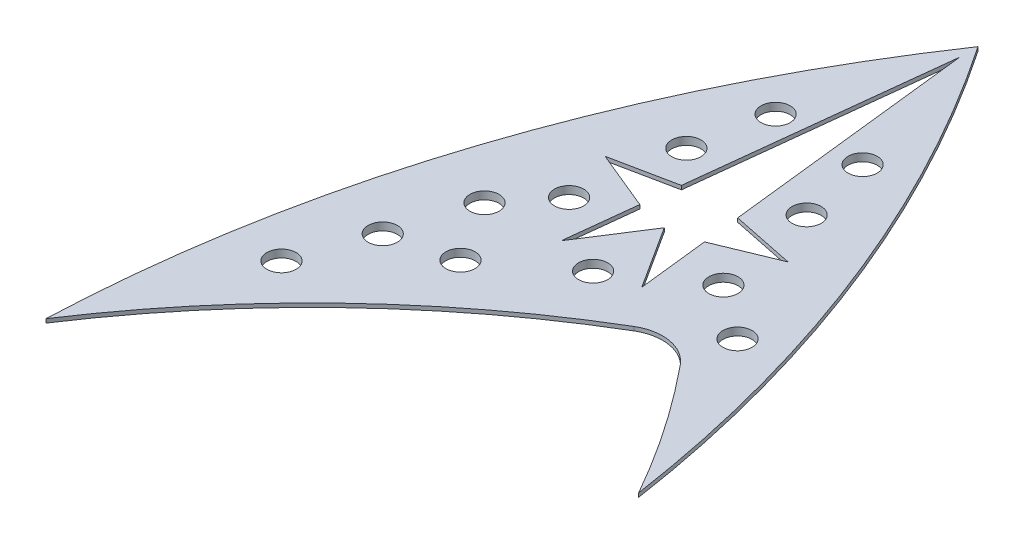
SolidWorks part; units mm, degrees
ref_plane "Front Plane" through (0, 0, 0) normal (0, 0, 1) x (1, 0, 0)
ref_plane "Top Plane" through (0, 0, 0) normal (0, 1, 0) x (1, 0, 0)
ref_plane "Right Plane" through (0, 0, 0) normal (1, 0, 0) x (0, 0, -1)
sketch "Sketch2" plane through (0, 0, 0) normal (0, 1, 0) x (1, 0, 0)
  line L10 (29.7241, 45.5525) -> (30.5369, 38.3256)
  line L11 (36.632, 48.4021) -> (29.7241, 45.5525)
  line L12 (29.1261, 50.8699) -> (35.6287, 49.5371)
  line L13 (26.9138, 70.5394) -> (29.1261, 50.8699)
  line L14 (21.5114, 50.8699) -> (23.7236, 70.5394)
  line L15 (15.0087, 49.5371) -> (21.5114, 50.8699)
  line L16 (20.9133, 45.5525) -> (14.0054, 48.4021)
  line L17 (19.7009, 34.7729) -> (20.9133, 45.5525)
  line L18 (25.3187, 43.524) -> (19.7009, 34.7729)
  line L19 (29.371, 37.2116) -> (25.3187, 43.524)
  line L29 (22.4239, 50.0361) -> (25.3187, 75.7743)
  line L30 (25.3187, 75.7743) -> (28.2135, 50.0361)
  line L31 (28.2135, 50.0361) -> (34.732, 48.7001)
  line L32 (34.732, 48.7001) -> (28.6462, 46.1896)
  line L33 (28.6462, 46.1896) -> (29.464, 38.9178)
  line L34 (29.464, 38.9178) -> (25.3187, 45.3751)
  line L35 (25.3187, 45.3751) -> (21.1734, 38.9178)
  line L36 (21.1734, 38.9178) -> (21.9913, 46.1896)
  line L37 (21.9913, 46.1896) -> (15.9054, 48.7001)
  line L39 (15.9054, 48.7001) -> (22.4239, 50.0361)
  arc A5 (47.6216, 20.4347) -> (38.3331, 34.0133) centre (-35, -26.1166) ccw
  arc A6 (38.3331, 34.0133) -> (32.5601, 35.0318) centre (34.8534, 31.16) ccw
  arc A7 (32.5601, 35.0318) -> (1.6083, 5.4751) centre (80.8889, -46.5628) ccw
  arc A8 (47.6216, 20.4347) -> (25.3187, 77.656) centre (-89.3626, 0) ccw
  arc A9 (25.3187, 77.656) -> (1.6083, 5.4751) centre (140, 0) ccw
  arc A23 (30.5369, 38.3256) -> (31.946, 37.5277) centre (31.5307, 38.4374) ccw
  arc A24 (42.6939, 32.5131) -> (40.2664, 35.5985) centre (-35, -26.1166) ccw
  arc A25 (40.2664, 35.5985) -> (31.946, 37.5277) centre (34.8534, 31.16) ccw
  arc A26 (42.6939, 32.5131) -> (37.9494, 47.8294) centre (-89.3626, 0) ccw
  arc A27 (37.9494, 47.8294) -> (36.632, 48.4021) centre (37.0133, 47.4777) ccw
  arc A28 (35.6287, 49.5371) -> (36.7569, 50.8909) centre (35.8295, 50.5167) ccw
  arc A29 (36.7569, 50.8909) -> (26.9138, 70.5394) centre (-89.3626, 0) ccw
  arc A30 (23.7236, 70.5394) -> (13.8806, 50.8909) centre (140, 0) ccw
  arc A31 (13.8806, 50.8909) -> (15.0087, 49.5371) centre (14.8079, 50.5167) ccw
  arc A32 (29.0619, 35.8249) -> (29.371, 37.2116) centre (28.5294, 36.6714) ccw
  arc A33 (29.0619, 35.8249) -> (4.727, 14.0437) centre (80.8889, -46.5628) ccw
  arc A34 (12.688, 47.8294) -> (4.727, 14.0437) centre (140, 0) ccw
  arc A35 (14.0054, 48.4021) -> (12.688, 47.8294) centre (13.6241, 47.4777) ccw
sketch "Sketch3" plane through (0, 0, 0) normal (0, 1, 0) x (1, 0, 0)
  point P0 (8.58, 22.733)
  point P1 (11.374, 30.353)
  point P3 (13.843, 38.354)
  point P4 (17.724, 43.18)
  point P5 (17.724, 32.004)
  point P6 (25.527, 37.846)
  point P7 (33.472, 43.307)
  point P8 (38.989, 39.243)
  point P9 (19.375, 53.594)
  point P10 (29.901, 61.2)
  point P11 (31.496, 53.848)
  point P12 (20.925, 61.225)
  dimension "D1" = 22.733
  dimension "D2" = 8.58
  dimension "D3" = 30.353
  dimension "D4" = 11.374
  dimension "D5" = 43.18
  dimension "D6" = 17.724
  dimension "D7" = 32.004
  dimension "D8" = 17.724
  dimension "D9" = 38.354
  dimension "D10" = 13.843
  dimension "D11" = 37.846
  dimension "D12" = 25.527
  dimension "D13" = 43.307
  dimension "D14" = 33.472
  dimension "D15" = 39.243
  dimension "D16" = 38.989
  dimension "D17" = 53.848
  dimension "D18" = 31.496
  dimension "D19" = 19.375
  dimension "D20" = 53.594
  dimension "D21" = 61.225
  dimension "D22" = 20.925
  dimension "D23" = 29.901
  dimension "D24" = 61.2
sketch "Sketch4" plane through (0, 0, 0) normal (0, 1, 0) x (1, 0, 0)
  line L0 (36.632, 48.4021) -> (29.7241, 45.5525) construction
  line L1 (29.7241, 45.5525) -> (30.5369, 38.3256) construction
  line L2 (26.9138, 70.5394) -> (29.1261, 50.8699) construction
  line L3 (29.1261, 50.8699) -> (35.6287, 49.5371) construction
  line L4 (20.9133, 45.5525) -> (14.0054, 48.4021) construction
  line L5 (29.371, 37.2116) -> (25.3187, 43.524) construction
  line L6 (25.3187, 43.524) -> (19.7009, 34.7729) construction
  line L7 (19.7009, 34.7729) -> (20.9133, 45.5525) construction
  line L8 (15.0087, 49.5371) -> (21.5114, 50.8699) construction
  line L9 (21.5114, 50.8699) -> (23.7236, 70.5394) construction
  line L10 (36.632, 48.4021) -> (29.7241, 45.5525)
  line L11 (29.7241, 45.5525) -> (30.5369, 38.3256)
  line L12 (26.9138, 70.5394) -> (29.1261, 50.8699)
  line L13 (29.1261, 50.8699) -> (35.6287, 49.5371)
  line L14 (20.9133, 45.5525) -> (14.0054, 48.4021)
  line L15 (29.371, 37.2116) -> (25.3187, 43.524)
  line L16 (25.3187, 43.524) -> (19.7009, 34.7729)
  line L17 (19.7009, 34.7729) -> (20.9133, 45.5525)
  line L18 (15.0087, 49.5371) -> (21.5114, 50.8699)
  line L19 (21.5114, 50.8699) -> (23.7236, 70.5394)
  arc A0 (30.5369, 38.3256) -> (31.946, 37.5277) centre (31.5307, 38.4374) ccw construction
  arc A1 (40.2664, 35.5985) -> (31.946, 37.5277) centre (34.8534, 31.16) ccw construction
  arc A2 (42.6939, 32.5131) -> (40.2664, 35.5985) centre (-35, -26.1166) ccw construction
  arc A3 (42.6939, 32.5131) -> (37.9494, 47.8294) centre (-89.3626, 0) ccw construction
  arc A4 (37.9494, 47.8294) -> (36.632, 48.4021) centre (37.0133, 47.4777) ccw construction
  arc A5 (35.6287, 49.5371) -> (36.7569, 50.8909) centre (35.8295, 50.5167) ccw construction
  arc A6 (36.7569, 50.8909) -> (26.9138, 70.5394) centre (-89.3626, 0) ccw construction
  arc A7 (14.0054, 48.4021) -> (12.688, 47.8294) centre (13.6241, 47.4777) ccw construction
  arc A8 (12.688, 47.8294) -> (4.727, 14.0437) centre (140, 0) ccw construction
  arc A9 (29.0619, 35.8249) -> (4.727, 14.0437) centre (80.8889, -46.5628) ccw construction
  arc A10 (29.0619, 35.8249) -> (29.371, 37.2116) centre (28.5294, 36.6714) ccw construction
  arc A11 (13.8806, 50.8909) -> (15.0087, 49.5371) centre (14.8079, 50.5167) ccw construction
  arc A12 (23.7236, 70.5394) -> (13.8806, 50.8909) centre (140, 0) ccw construction
  arc A13 (30.5369, 38.3256) -> (31.946, 37.5277) centre (31.5307, 38.4374) ccw
  arc A14 (40.2664, 35.5985) -> (31.946, 37.5277) centre (34.8534, 31.16) ccw
  arc A15 (42.6939, 32.5131) -> (40.2664, 35.5985) centre (-35, -26.1166) ccw
  arc A16 (42.6939, 32.5131) -> (37.9494, 47.8294) centre (-89.3626, 0) ccw
  arc A17 (37.9494, 47.8294) -> (36.632, 48.4021) centre (37.0133, 47.4777) ccw
  arc A18 (35.6287, 49.5371) -> (36.7569, 50.8909) centre (35.8295, 50.5167) ccw
  arc A19 (36.7569, 50.8909) -> (26.9138, 70.5394) centre (-89.3626, 0) ccw
  arc A20 (14.0054, 48.4021) -> (12.688, 47.8294) centre (13.6241, 47.4777) ccw
  arc A21 (12.688, 47.8294) -> (4.727, 14.0437) centre (140, 0) ccw
  arc A22 (29.0619, 35.8249) -> (4.727, 14.0437) centre (80.8889, -46.5628) ccw
  arc A23 (29.0619, 35.8249) -> (29.371, 37.2116) centre (28.5294, 36.6714) ccw
  arc A24 (13.8806, 50.8909) -> (15.0087, 49.5371) centre (14.8079, 50.5167) ccw
  arc A25 (23.7236, 70.5394) -> (13.8806, 50.8909) centre (140, 0) ccw
  circle A26 centre (8.58, 22.733) radius 1.5
  circle A27 centre (11.374, 30.353) radius 1.5
  circle A28 centre (13.843, 38.354) radius 1.5
  circle A29 centre (17.724, 32.004) radius 1.5
  circle A30 centre (17.724, 43.18) radius 1.5
  circle A31 centre (19.375, 53.594) radius 1.5
  circle A32 centre (20.925, 61.225) radius 1.5
  circle A33 centre (33.472, 43.307) radius 1.5
  circle A34 centre (38.989, 39.243) radius 1.5
  circle A35 centre (31.496, 53.848) radius 1.5
  circle A36 centre (29.901, 61.2) radius 1.5
  circle A37 centre (25.527, 37.846) radius 1.5
extrude "Boss-Extrude1" add sketch "Sketch4" along normal blind 0.4
sketch "Sketch5" plane through (0, 0.4, 0) normal (0, 1, 0) x (1, 0, 0)
  line L0 (22.4239, 50.0361) -> (25.3187, 75.7743) construction
  line L1 (25.3187, 75.7743) -> (28.2135, 50.0361) construction
  line L2 (28.2135, 50.0361) -> (34.732, 48.7001) construction
  line L3 (34.732, 48.7001) -> (28.6462, 46.1896) construction
  line L4 (28.6462, 46.1896) -> (29.464, 38.9178) construction
  line L5 (29.464, 38.9178) -> (25.3187, 45.3751) construction
  line L6 (25.3187, 45.3751) -> (21.1734, 38.9178) construction
  line L7 (21.1734, 38.9178) -> (21.9913, 46.1896) construction
  line L8 (21.9913, 46.1896) -> (15.9054, 48.7001) construction
  line L9 (15.9054, 48.7001) -> (22.4239, 50.0361) construction
  line L10 (22.4239, 50.0361) -> (25.3187, 75.7743)
  line L11 (25.3187, 75.7743) -> (28.2135, 50.0361)
  line L12 (28.2135, 50.0361) -> (34.732, 48.7001)
  line L13 (34.732, 48.7001) -> (28.6462, 46.1896)
  line L14 (28.6462, 46.1896) -> (29.464, 38.9178)
  line L15 (29.464, 38.9178) -> (25.3187, 45.3751)
  line L16 (25.3187, 45.3751) -> (21.1734, 38.9178)
  line L17 (21.1734, 38.9178) -> (21.9913, 46.1896)
  line L18 (21.9913, 46.1896) -> (15.9054, 48.7001)
  line L19 (15.9054, 48.7001) -> (22.4239, 50.0361)
  circle A0 centre (8.58, 22.733) radius 1.5 construction
  circle A1 centre (11.374, 30.353) radius 1.5 construction
  circle A2 centre (17.724, 43.18) radius 1.5 construction
  circle A3 centre (13.843, 38.354) radius 1.5 construction
  circle A4 centre (17.724, 32.004) radius 1.5 construction
  circle A5 centre (38.989, 39.243) radius 1.5 construction
  circle A6 centre (33.472, 43.307) radius 1.5 construction
  circle A7 centre (31.496, 53.848) radius 1.5 construction
  circle A8 centre (29.901, 61.2) radius 1.5 construction
  circle A9 centre (20.925, 61.225) radius 1.5 construction
  circle A10 centre (19.375, 53.594) radius 1.5 construction
  arc A11 (25.3187, 77.656) -> (1.6083, 5.4751) centre (140, 0) ccw construction
  arc A12 (32.5601, 35.0318) -> (1.6083, 5.4751) centre (80.8889, -46.5628) ccw construction
  arc A13 (38.3331, 34.0133) -> (32.5601, 35.0318) centre (34.8534, 31.16) ccw construction
  arc A14 (47.6216, 20.4347) -> (38.3331, 34.0133) centre (-35, -26.1166) ccw construction
  arc A15 (47.6216, 20.4347) -> (25.3187, 77.656) centre (-89.3626, 0) ccw construction
  circle A16 centre (8.58, 22.733) radius 1.5
  circle A17 centre (11.374, 30.353) radius 1.5
  circle A18 centre (17.724, 43.18) radius 1.5
  circle A19 centre (13.843, 38.354) radius 1.5
  circle A20 centre (17.724, 32.004) radius 1.5
  circle A21 centre (38.989, 39.243) radius 1.5
  circle A22 centre (33.472, 43.307) radius 1.5
  circle A23 centre (31.496, 53.848) radius 1.5
  circle A24 centre (29.901, 61.2) radius 1.5
  circle A25 centre (20.925, 61.225) radius 1.5
  circle A26 centre (19.375, 53.594) radius 1.5
  arc A27 (25.3187, 77.656) -> (1.6083, 5.4751) centre (140, 0) ccw
  arc A28 (32.5601, 35.0318) -> (1.6083, 5.4751) centre (80.8889, -46.5628) ccw
  arc A29 (38.3331, 34.0133) -> (32.5601, 35.0318) centre (34.8534, 31.16) ccw
  arc A30 (47.6216, 20.4347) -> (38.3331, 34.0133) centre (-35, -26.1166) ccw
  arc A31 (47.6216, 20.4347) -> (25.3187, 77.656) centre (-89.3626, 0) ccw
  circle A32 centre (25.527, 37.846) radius 1.5 construction
  circle A33 centre (25.527, 37.846) radius 1.5
extrude "Boss-Extrude2" add sketch "Sketch5" along normal blind 0.4
